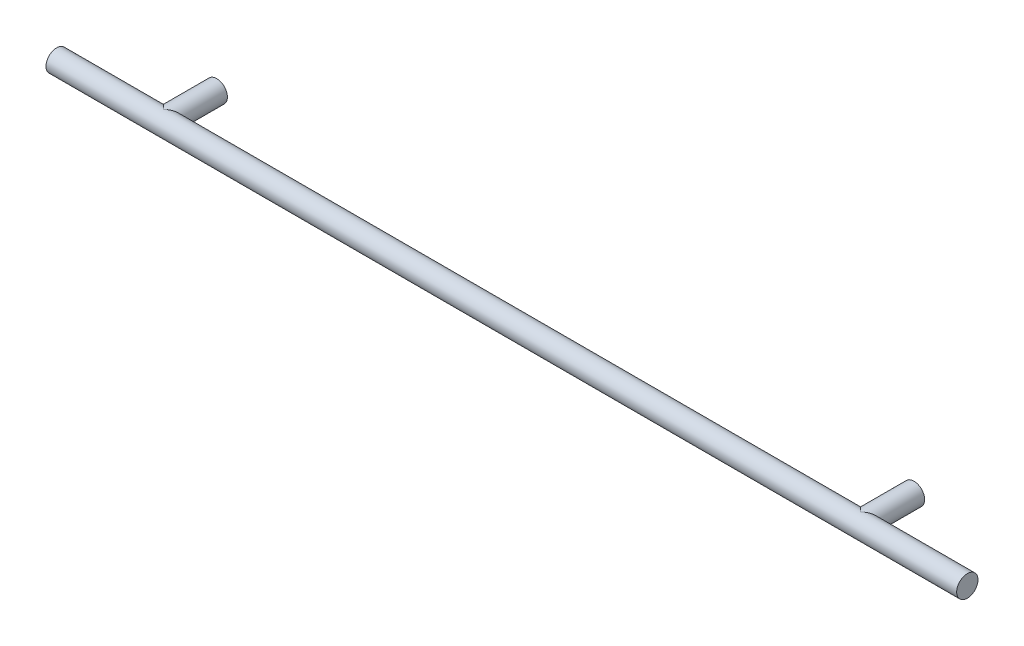
SolidWorks part; units mm, degrees
material "1023 Carbon Steel Sheet (SS)"
ref_plane "Front Plane" through (0, 0, 0) normal (0, 0, 1) x (1, 0, 0)
ref_plane "Top Plane" through (0, 0, 0) normal (0, 1, 0) x (1, 0, 0)
ref_plane "Right Plane" through (0, 0, 0) normal (1, 0, 0) x (0, 0, -1)
sketch "Sketch1" plane through (0, 0, 0) normal (0, 0, 1) x (1, 0, 0)
  line L0 (0, 0) -> (0, 300.5709) construction
  circle A0 centre (-155.575, 0) radius 4.7625
  circle A1 centre (155.575, 0) radius 4.7625
  point P7 (0, 0)
  dimension "D2" = 9.525
  dimension "D1" = 311.15
sketch "Sketch2" plane through (0, 0, 0) normal (1, 0, 0) x (0, 0, -1)
  circle A0 centre (-23.8125, 0) radius 4.7625
  point P2 (0, 0)
  dimension "D1" = 9.525
  dimension "D2" = 23.8125
extrude "Boss-Extrude1" add sketch "Sketch2" along normal mid plane 406.4
extrude "Boss-Extrude2" add sketch "Sketch1" along normal up to next
